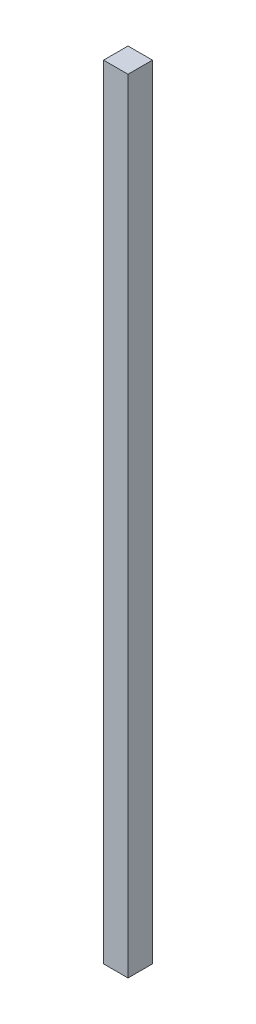
SolidWorks part; units mm, degrees
material "Balsa"
ref_plane "Front Plane" through (0, 0, 0) normal (0, 0, 1) x (1, 0, 0)
ref_plane "Top Plane" through (0, 0, 0) normal (0, 1, 0) x (1, 0, 0)
ref_plane "Right Plane" through (0, 0, 0) normal (1, 0, 0) x (0, 0, -1)
sketch "Sketch1" plane through (0, 0, 0) normal (0, 1, 0) x (1, 0, 0)
  line L1 (-3.175, -3.175) -> (3.175, -3.175)
  line L2 (-3.175, -3.175) -> (-3.175, 3.175)
  line L3 (-3.175, 3.175) -> (3.175, 3.175)
  line L4 (3.175, -3.175) -> (3.175, 3.175)
  line L5 (-3.175, -3.175) -> (3.175, 3.175) construction
  line L6 (-3.175, 3.175) -> (3.175, -3.175) construction
  point P0 (0, 0)
  dimension "D1" = 6.35
extrude "Boss-Extrude1" add sketch "Sketch1" along normal blind 203.2
